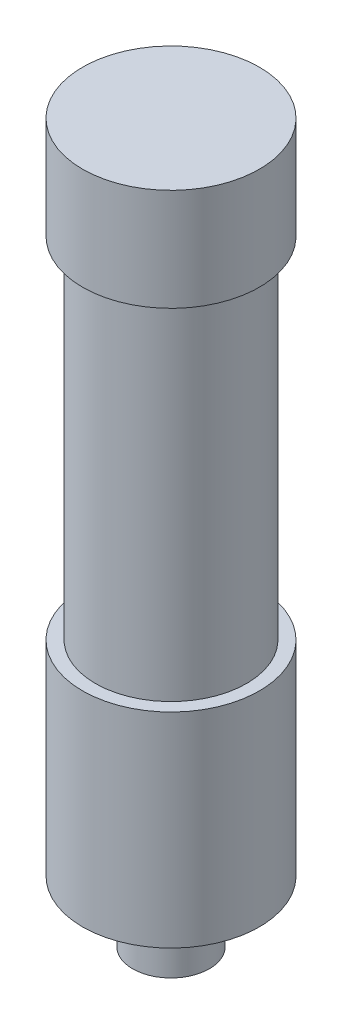
SolidWorks part; units mm, degrees
ref_plane "Front" through (0, 0, 0) normal (0, 0, 1) x (1, 0, 0)
ref_plane "Top" through (0, 0, 0) normal (0, 1, 0) x (1, 0, 0)
ref_plane "Right" through (0, 0, 0) normal (1, 0, 0) x (0, 0, -1)
sketch "Sketch1" plane through (0, 0, 0) normal (0, 0, 1) x (1, 0, 0)
  line L0 (0, 0) -> (0, 25.4) construction
  line L1 (0, 25.4) -> (-10.9855, 25.4)
  line L2 (-10.9855, 25.4) -> (-10.9855, 12.7)
  line L3 (-10.9855, 12.7) -> (-9.398, 12.7)
  line L4 (-9.398, 12.7) -> (-9.398, -30.734)
  line L5 (-9.398, -30.734) -> (-10.9855, -30.734)
  line L6 (-10.9855, -30.734) -> (-10.9855, -56.134)
  line L7 (-10.9855, -56.134) -> (-4.7625, -56.134)
  line L8 (-4.7625, -56.134) -> (-4.7625, -63.754)
  line L9 (-4.7625, -63.754) -> (0, -63.754)
  line L10 (0, 25.4) -> (0, -92.7133) construction
  line L11 (0, 25.4) -> (0, -63.754)
  dimension "D1" = 10.9855
  dimension "D2" = 21.971
  dimension "D3" = 81.534
  dimension "D4" = 7.62
  dimension "D5" = 1.5875
  dimension "D6" = 9.525
  dimension "D7" = 25.4
  dimension "D8" = 12.7
  dimension "D9" = 25.4
revolve "Revolve1" add sketch "Sketch1" angle 360 about L10
